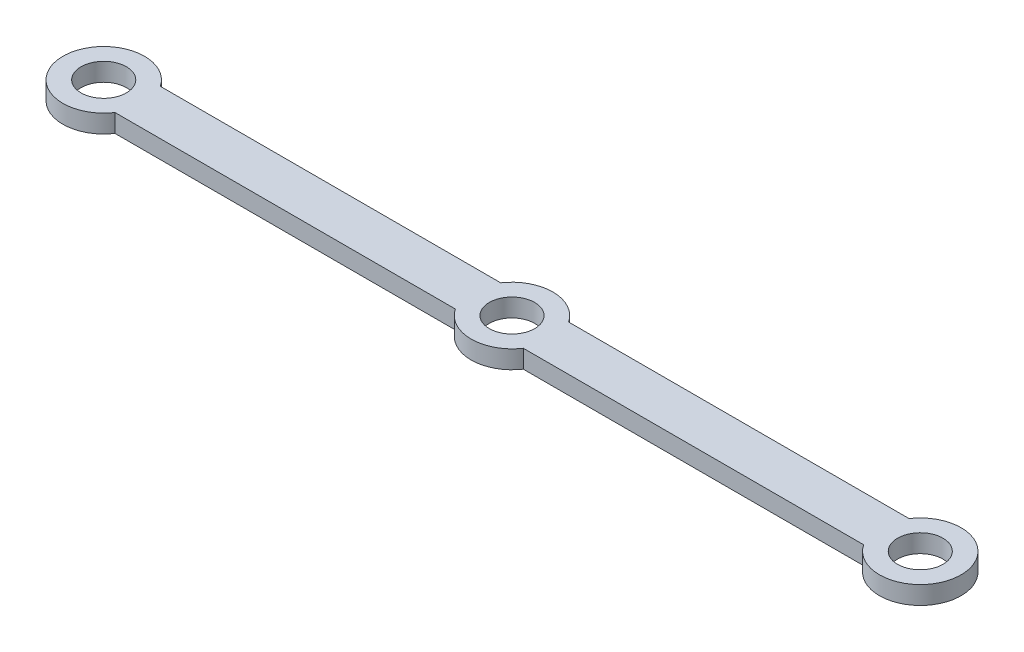
SolidWorks part; units mm, degrees
ref_plane "Front Plane" through (0, 0, 0) normal (0, 0, 1) x (1, 0, 0)
ref_plane "Top Plane" through (0, 0, 0) normal (0, 1, 0) x (1, 0, 0)
ref_plane "Right Plane" through (0, 0, 0) normal (1, 0, 0) x (0, 0, -1)
sketch "Sketch1" plane through (0, 0, 0) normal (0, 1, 0) x (1, 0, 0)
  line L0 (0, 0) -> (90, 0) construction
  line L1 (3.7417, 2.5) -> (86.2583, 2.5)
  line L2 (3.7417, -2.5) -> (86.2583, -2.5)
  circle A0 centre (0, 0) radius 4.5
  circle A1 centre (45, 0) radius 4.5
  circle A2 centre (90, 0) radius 4.5
  circle A3 centre (0, 0) radius 2.5
  circle A4 centre (45, 0) radius 2.5
  circle A5 centre (90, 0) radius 2.5
  dimension "D1" = 5
  dimension "D2" = 9
  dimension "D3" = 90
extrude "Boss-Extrude1" add sketch "Sketch1" along normal blind 2
